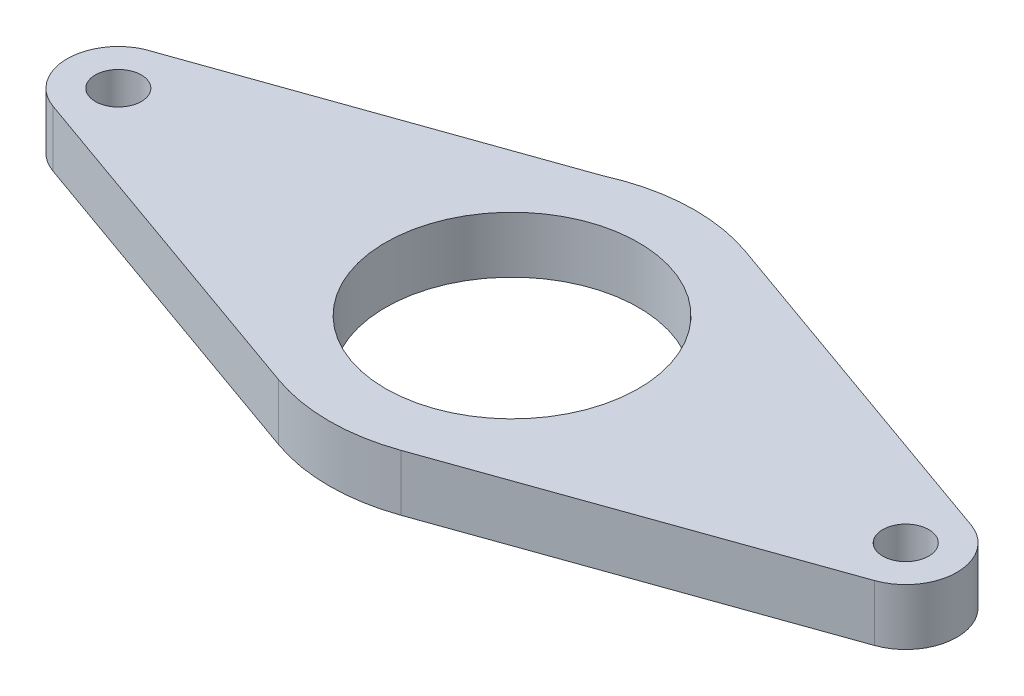
SolidWorks part; units mm, degrees
ref_plane "Front Plane" through (0, 0, 0) normal (0, 0, 1) x (1, 0, 0)
ref_plane "Top Plane" through (0, 0, 0) normal (0, 1, 0) x (1, 0, 0)
ref_plane "Right Plane" through (0, 0, 0) normal (1, 0, 0) x (0, 0, -1)
sketch "Sketch1" plane through (0, 0, 0) normal (0, 1, 0) x (1, 0, 0)
  line L0 (0, 0) -> (44.45, 0)
  line L1 (0, 0) -> (-44.45, 0)
  line L3 (6.9004, 19.4497) -> (46.381, 5.4426)
  line L4 (-46.381, -5.4426) -> (-6.9004, -19.4497)
  line L5 (6.9004, -19.4497) -> (46.381, -5.4426)
  line L6 (-8.4426, 18.8316) -> (-46.8125, 5.2697)
  circle A0 centre (0, 0) radius 14.2875
  circle A1 centre (0, 0) radius 20.6375
  circle A2 centre (-44.45, 0) radius 2.6
  circle A3 centre (44.45, 0) radius 2.6
  circle A4 centre (-44.45, 0) radius 5.775
  circle A5 centre (44.45, 0) radius 5.775
  dimension "D1" = 28.575
  dimension "D5" = 5.2
  dimension "D6" = 5.2
  dimension "1.75" = 44.45
  dimension "D4" = 44.45
  dimension "D2" = 6.35
  dimension "D7" = 3.175
  dimension "D8" = 3.175
extrude "Boss-Extrude2" add sketch "Sketch1" along normal blind 6.35
